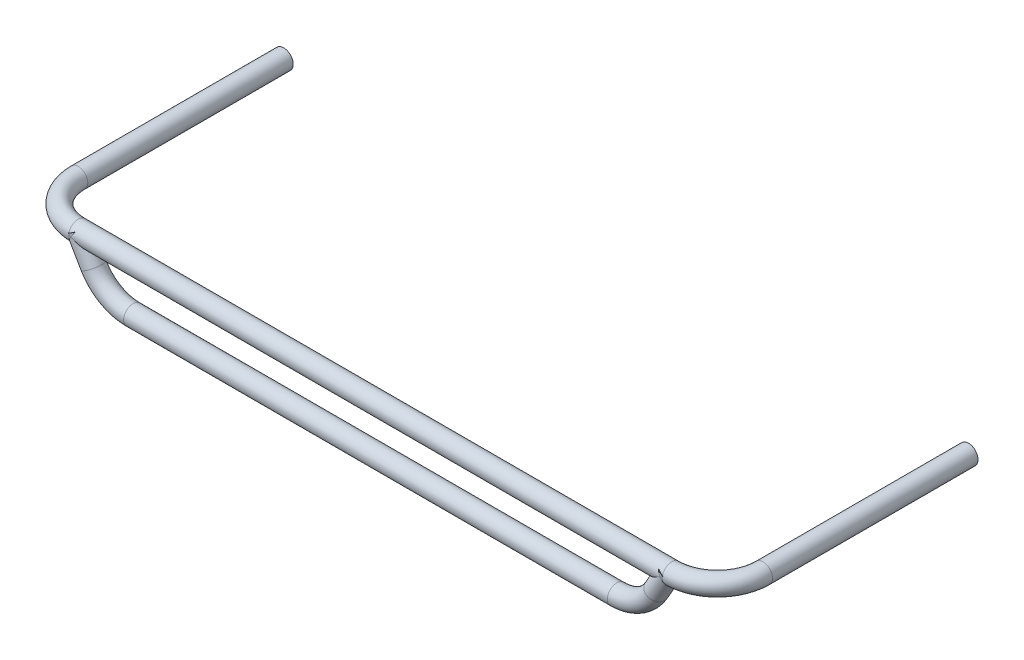
SolidWorks part; units mm, degrees
ref_plane "Front Plane" through (0, 0, 0) normal (0, 0, 1) x (1, 0, 0)
ref_plane "Top Plane" through (0, 0, 0) normal (0, 1, 0) x (1, 0, 0)
ref_plane "Right Plane" through (0, 0, 0) normal (1, 0, 0) x (0, 0, -1)
sketch "Sketch1" plane through (0, 0, 0) normal (0, 1, 0) x (1, 0, 0)
  line L0 (-260, -140) -> (260, -140)
  line L1 (-300, -100) -> (-300, 0)
  line L2 (300, -100) -> (300, 0)
  arc A0 (300, -100) -> (260, -140) centre (260, -100) cw
  arc A1 (-300, -100) -> (-260, -140) centre (-260, -100) ccw
  point P10 (300, -140)
  point P13 (-300, -140)
  dimension "D4" = 40
  dimension "D1" = 600
  dimension "D2" = 140
  dimension "D3" = 300
sketch "Sketch2" plane through (0, 0, 0) normal (0, 0, 1) x (1, 0, 0)
  circle A0 centre (300, 0) radius 8.35
  dimension "D1" = 16.7
sweep "Sweep1" add profiles "Sketch2" path "Sketch1"
ref_plane "Plane1" through (0, 0, 140) normal (0, 0, 1) x (1, 0, 0)
sketch "Sketch3" plane through (0, 0, 140) normal (0, 0, 1) x (1, 0, 0)
  line L0 (-211.906, -40) -> (211.906, -40)
  line L1 (-246.547, -20) -> (-252.8533, -9.0772)
  line L2 (246.547, -20) -> (252.8533, -9.0772)
  line L3 (0, 0) -> (0, -97.158) construction
  arc A0 (246.547, -20) -> (211.906, -40) centre (211.906, 0) cw
  arc A1 (-246.547, -20) -> (-211.906, -40) centre (-211.906, 0) ccw
  point P7 (0, -40)
  point P13 (235, -40)
  point P16 (-235, -40)
  dimension "D5" = 40
  dimension "D1" = 470
  dimension "D2" = 120
  dimension "D3" = 120
  dimension "D4" = 40
ref_plane "Plane2" through (-252.8533, -9.0772, 140) normal (-0.5, 0.866, 0) x (0.866, 0.5, 0)
sketch "Sketch4" plane through (-252.8533, -9.0772, 140) normal (-0.5, 0.866, 0) x (0.866, 0.5, 0)
  circle A0 centre (0, 0) radius 8.35
  dimension "D1" = 16.7
sweep "Sweep2" add profiles "Sketch4" path "Sketch3"
sketch "Sketch5" plane through (-59.2828, 102.6807, 0) normal (-0.5, 0.866, 0) x (0.866, 0.5, 0)
  arc A1 (-217.4645, -134.2466) -> (-217.4645, -145.7534) centre (-223.516, -140) ccw
  arc A2 (-217.4645, -134.2466) -> (-217.4645, -145.7534) centre (-223.516, -140) ccw
  ellipse E1 centre (-205.3615, -140) end of major axis (-188.6615, -140) minor radius 8.35 (-217.4645, -134.2466) -> (-217.4645, -145.7534) ccw
  ellipse E2 centre (-205.3615, -140) end of major axis (-188.6615, -140) minor radius 8.35 (-217.4645, -134.2466) -> (-217.4645, -145.7534) ccw
  dimension "D1" = 0
extrude "Boss-Extrude2" add sketch "Sketch5" along normal blind 13
sketch "Sketch6" plane through (59.2828, 102.6807, 0) normal (0.5, 0.866, 0) x (0.866, -0.5, 0)
  arc A1 (217.4645, -145.7534) -> (217.4645, -134.2466) centre (223.516, -140) ccw
  arc A2 (217.4645, -145.7534) -> (217.4645, -134.2466) centre (223.516, -140) ccw
  ellipse E1 centre (205.3615, -140) end of major axis (222.0615, -140) minor radius 8.35 (217.4645, -145.7534) -> (217.4645, -134.2466) ccw
  ellipse E2 centre (205.3615, -140) end of major axis (222.0615, -140) minor radius 8.35 (217.4645, -145.7534) -> (217.4645, -134.2466) ccw
  dimension "D1" = 0
extrude "Boss-Extrude3" add sketch "Sketch6" along normal blind 13
sketch "Sketch7" plane through (0, 0, 0) normal (0, 0, -1) x (-1, 0, 0)
  circle A1 centre (-300, 0) radius 8.35
  circle A2 centre (-300, 0) radius 8.35
  dimension "D1" = 0
extrude "Boss-Extrude4" add sketch "Sketch7" along normal blind 80
sketch "Sketch8" plane through (0, 0, 0) normal (0, 0, -1) x (-1, 0, 0)
  circle A1 centre (300, 0) radius 8.35
  circle A2 centre (300, 0) radius 8.35
  dimension "D1" = 0
extrude "Boss-Extrude5" add sketch "Sketch8" along normal blind 80
